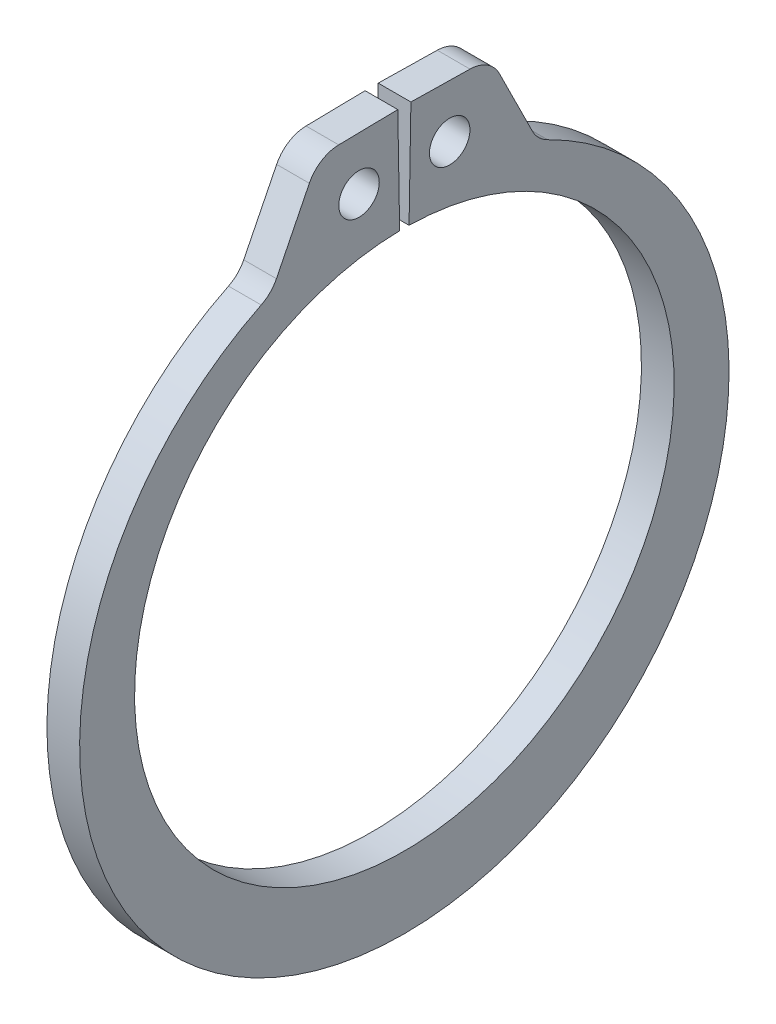
SolidWorks part; units mm, degrees
material "Cast Carbon Steel"
ref_plane "Front" through (0, 0, 0) normal (0, 0, 1) x (1, 0, 0)
ref_plane "Top" through (0, 0, 0) normal (0, 1, 0) x (1, 0, 0)
ref_plane "Right" through (0, 0, 0) normal (1, 0, 0) x (0, 0, -1)
sketch "Sketch1" plane through (0, 0, 0) normal (1, 0, 0) x (0, 0, -1)
  line L0 (0, 0) -> (0, 8.8011) construction
  line L1 (-0.1536, 8.7998) -> (-0.2139, 12.2536)
  line L2 (0.2139, 12.2536) -> (2.8043, 12.2084)
  line L3 (2.8043, 12.2084) -> (4.342, 9.1152)
  line L4 (0.1536, 8.7998) -> (0.2139, 12.2536)
  line L5 (-0.2139, 12.2536) -> (-2.8043, 12.2084)
  line L6 (-2.8043, 12.2084) -> (-4.342, 9.1152)
  line L7 (-4.342, 9.1152) -> (-3.7849, 7.9457) construction
  line L8 (4.342, 9.1152) -> (3.7849, 7.9457) construction
  line L9 (0, -8.8011) -> (0, -11.1379) construction
  line L10 (-2.8043, 12.2084) -> (-0.1536, 8.7998) construction
  line L11 (0, 8.8011) -> (0, 12.2555) construction
  circle A0 centre (0, 0) radius 8.8011 construction
  arc A1 (-0.1536, 8.7998) -> (0.1536, 8.7998) centre (0, 0) ccw
  circle A3 centre (0, 0) radius 13.589 construction
  circle A4 centre (-1.4789, 10.5041) radius 0.6604
  circle A5 centre (1.4789, 10.5041) radius 0.6604
  arc A6 (-4.342, 9.1152) -> (4.342, 9.1152) centre (0, -0.5459) ccw
  point P0 (0, -11.1379)
  dimension "A" = 17.6022
  dimension "D2" = 2.5908
  dimension "L" = 27.178
  dimension "Hole" = 1.3208
  dimension "Smin" = 1.2954
  dimension "Smax" = 2.3368
  dimension "H" = 3.4544
  dimension "Angle" = 1
extrude "Extrude1" add sketch "Sketch1" along normal mid plane 1.0668
fillet "Fillet1" radius 1.0922 4 edges at (0, 9.1152, 4.342) (0, 9.1152, -4.342) (0, 12.2084, 2.8043) (0, 12.2084, -2.8043)
sketch "Sketch2" plane through (0, 0, 0) normal (0, 0, 1) x (1, 0, 0)
  line L0 (-5.9182, 0) -> (15.4178, 0)
  line L1 (15.4178, 0) -> (15.4178, -9.525)
  line L2 (-0.5842, -9.525) -> (-5.334, -9.525)
  line L3 (15.4178, -9.525) -> (0.5842, -9.525)
  line L4 (0.5842, -9.525) -> (0.5842, -8.9408)
  line L5 (0.5842, -8.9408) -> (-0.5842, -8.9408)
  line L6 (-0.5842, -8.9408) -> (-0.5842, -9.525)
  line L7 (-0.5842, -9.525) -> (-5.9182, -9.525) construction
  line L8 (-5.9182, -9.525) -> (-5.9182, 0) construction
  line L9 (15.4178, 0) -> (76.391, 0) construction
  line L10 (-5.334, -9.525) -> (-5.9182, -8.9408)
  line L11 (-5.9182, -8.9408) -> (-5.9182, 0)
  point P10 (0, -8.9408)
  dimension "D1" = 45
  dimension "Dg" = 17.8816
  dimension "Ds" = 19.05
  dimension "W" = 1.1684
  dimension "D2" = 21.336
  dimension "D3" = 5.334
revolve "Revolve1" [suppressed] add sketch "Sketch2" angle 360 about L9
delete or keep bodies "Body-Delete1" [suppressed] type delete bodies bodies 122
equation "\"D2@Sketch2\" = \"D1@Extrude1\"*20"
equation "\"D3@Sketch2\" = \"D2@Sketch2\"/4"
equation "\"D2@Sketch1\" = \"H@Sketch1\"*.75"
